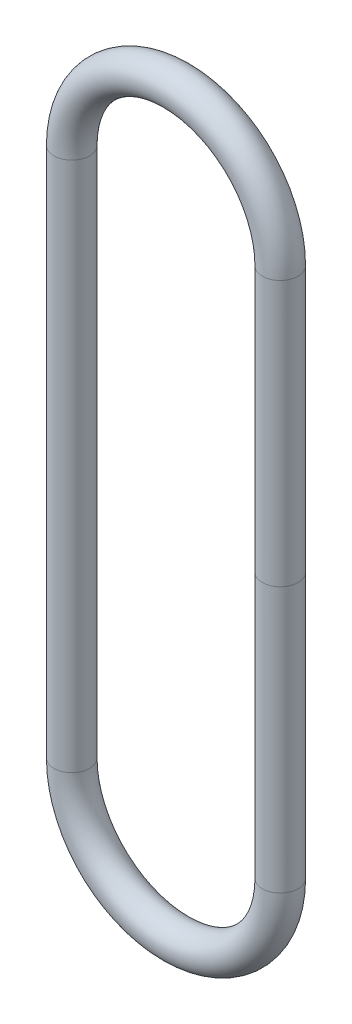
SolidWorks part; units mm, degrees
material "Rubber"
ref_plane "Front Plane" through (0, 0, 0) normal (0, 0, 1) x (1, 0, 0)
ref_plane "Top Plane" through (0, 0, 0) normal (0, 1, 0) x (1, 0, 0)
ref_plane "Right Plane" through (0, 0, 0) normal (1, 0, 0) x (0, 0, -1)
sketch "Sketch1" plane through (0, 0, 0) normal (0, 0, 1) x (1, 0, 0)
  line L0 (0, -13.175) -> (0, 13.175) construction
  line L1 (-4.2895, -13.175) -> (-4.2895, 13.175)
  line L2 (4.2895, -13.175) -> (4.2895, 13.175)
  arc A0 (-4.2895, -13.175) -> (4.2895, -13.175) centre (0, -13.175) ccw
  arc A1 (4.2895, 13.175) -> (-4.2895, 13.175) centre (0, 13.175) ccw
  circle A4 centre (0, 0) radius 12.677 construction
  point P2 (0, 0)
sketch "Sketch2" plane through (0, 0, 0) normal (0, 1, 0) x (1, 0, 0)
  line L0 (0, 0) -> (4.2895, 0) construction
  circle A0 centre (5.1785, 0) radius 0.889
  dimension "D1" = 1.778
sweep "-019 O-Ring" add profiles "Sketch2" path "Sketch1"
equation "\"Inner Diameter\"= \"D3@Sketch1\" / pi"
